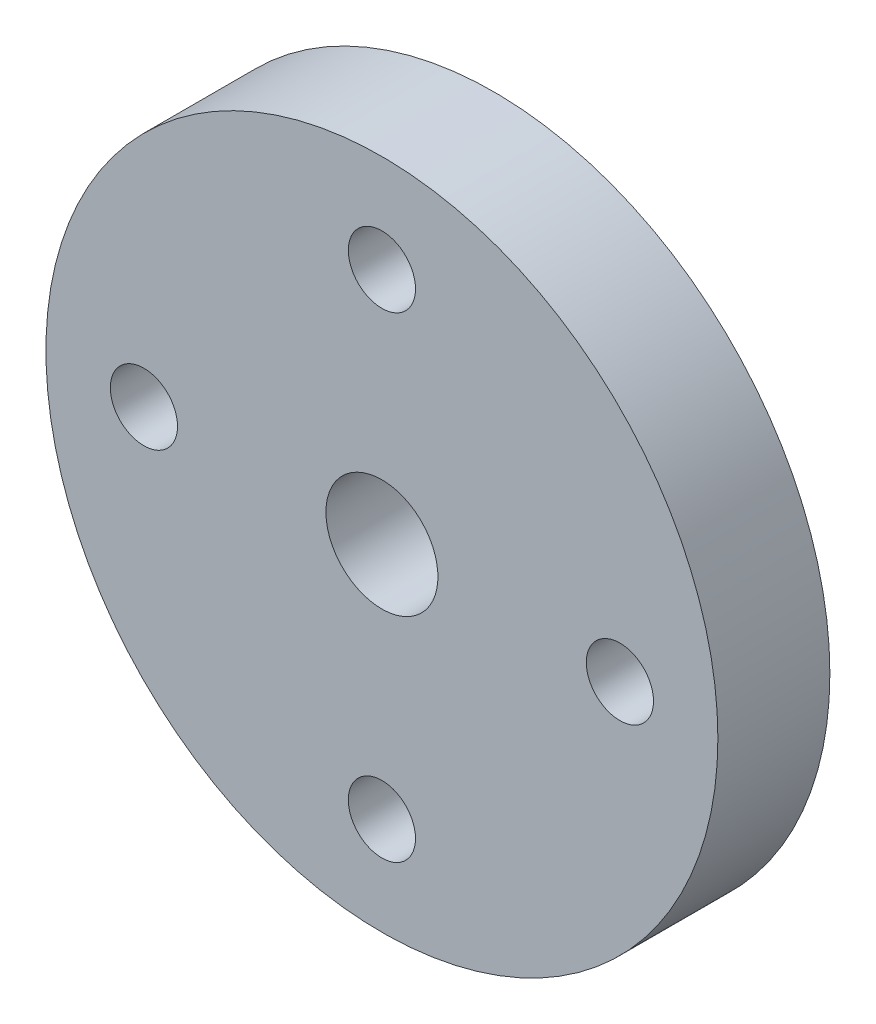
SolidWorks part; units mm, degrees
ref_plane "Front Plane" through (0, 0, 0) normal (0, 0, 1) x (1, 0, 0)
ref_plane "Top Plane" through (0, 0, 0) normal (0, 1, 0) x (1, 0, 0)
ref_plane "Right Plane" through (0, 0, 0) normal (1, 0, 0) x (0, 0, -1)
sketch "Sketch1" plane through (0, 0, 0) normal (0, 0, 1) x (1, 0, 0)
  circle A0 centre (0, 0) radius 30
  circle A2 centre (0, 21.25) radius 3
  circle A5 centre (21.25, 0) radius 3
  circle A6 centre (0, -21.25) radius 3
  circle A7 centre (-21.25, 0) radius 3
  point P2 (0, 0)
  dimension "D2" = 60
  dimension "D3" = 6
  dimension "D4" = 21.25
  dimension "D5" = 42.5
  dimension "D1" = 4
extrude "Boss-Extrude3" add sketch "Sketch1" along normal blind 10
sketch "Sketch2" plane through (0, 0, 0) normal (0, 0, -1) x (-1, 0, 0)
  circle A0 centre (0, 0) radius 10
  dimension "D1" = 20
extrude "Boss-Extrude4" add sketch "Sketch2" along normal blind 10
sketch "Sketch3" plane through (0, 0, -10) normal (0, 0, -1) x (-1, 0, 0)
  circle A0 centre (0, 0) radius 5
  dimension "D1" = 10
extrude "Cut-Extrude1" cut sketch "Sketch3" against normal through all
